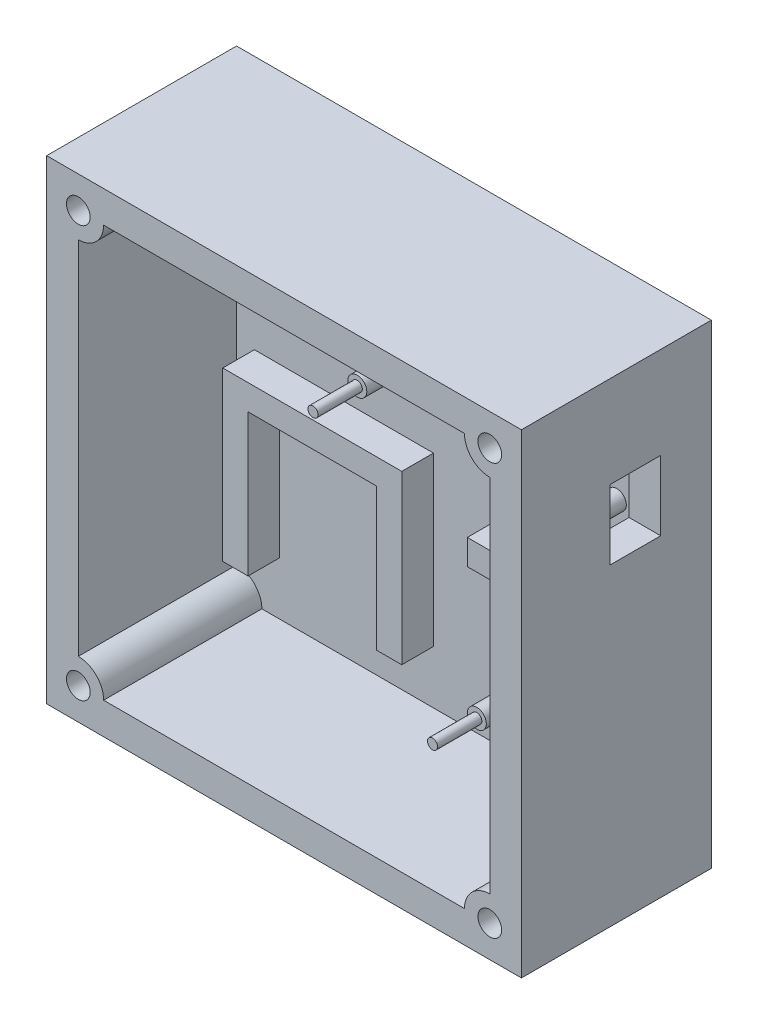
SolidWorks part; units mm, degrees
ref_plane "Front Plane" through (0, 0, 0) normal (0, 0, 1) x (1, 0, 0)
ref_plane "Top Plane" through (0, 0, 0) normal (0, 1, 0) x (1, 0, 0)
ref_plane "Right Plane" through (0, 0, 0) normal (1, 0, 0) x (0, 0, -1)
sketch "Sketch1" plane through (0, 0, 0) normal (0, 0, 1) x (1, 0, 0)
  line L1 (-47.625, -47.625) -> (47.625, -47.625)
  line L2 (-47.625, -47.625) -> (-47.625, 47.625)
  line L3 (-47.625, 47.625) -> (47.625, 47.625)
  line L4 (47.625, -47.625) -> (47.625, 47.625)
  line L5 (-47.625, -47.625) -> (47.625, 47.625) construction
  line L6 (-47.625, 47.625) -> (47.625, -47.625) construction
  point P0 (0, 0)
  dimension "D1" = 95.25
  dimension "D2" = 95.25
extrude "Boss-Extrude1" add sketch "Sketch1" along normal blind 38.1
shell "Shell1" thickness 6.35
ref_plane "Plane1" through (0, 0, 38.1) normal (0, 0, 1) x (1, 0, 0)
sketch "Sketch2" plane through (0, 0, 38.1) normal (0, 0, 1) x (1, 0, 0)
  line L0 (41.275, 41.275) -> (-41.275, 41.275) construction
  line L1 (-41.275, 41.275) -> (-41.275, -41.275) construction
  line L2 (-41.275, 41.275) -> (-36.195, 41.275)
  line L3 (-41.275, 41.275) -> (-41.275, 36.195)
  line L4 (41.275, 41.275) -> (-41.275, 41.275) construction
  line L5 (41.275, -41.275) -> (41.275, 41.275) construction
  line L6 (36.195, 41.275) -> (41.275, 41.275)
  line L7 (41.275, 41.275) -> (41.275, 36.195)
  line L8 (-41.275, -41.275) -> (41.275, -41.275) construction
  line L9 (41.275, -36.195) -> (41.275, -41.275)
  line L10 (41.275, -41.275) -> (36.195, -41.275)
  line L11 (-41.275, -41.275) -> (41.275, -41.275) construction
  line L12 (-41.275, -36.195) -> (-41.275, -41.275)
  line L13 (-41.275, -41.275) -> (-36.195, -41.275)
  arc A0 (-36.195, 41.275) -> (-41.275, 36.195) centre (-41.275, 41.275) cw
  arc A1 (36.195, 41.275) -> (41.275, 36.195) centre (41.275, 41.275) ccw
  arc A2 (41.275, -36.195) -> (36.195, -41.275) centre (41.275, -41.275) ccw
  arc A3 (-41.275, -36.195) -> (-36.195, -41.275) centre (-41.275, -41.275) cw
  dimension "D1" = 5.08
extrude "Boss-Extrude2" add sketch "Sketch2" against normal up to surface (31.75 mm away) up to face at (0, 0, 6.35)
sketch "Sketch3" plane through (0, 0, 6.35) normal (0, 0, 1) x (1, 0, 0)
  line L0 (41.275, -36.195) -> (41.275, 36.195) construction
  circle A0 centre (35.0157, 31.115) radius 1.905
  circle A1 centre (-10.7043, 31.115) radius 1.016
  circle A2 centre (-10.7043, 13.335) radius 1.905
  circle A3 centre (35.0157, 13.335) radius 1.905
  dimension "D1" = 3.81
  dimension "D2" = 2.032
  dimension "D3" = 6.2593
  dimension "D4" = 17.78
  dimension "D5" = 45.72
  dimension "D6" = 10.16
extrude "Boss-Extrude3" add sketch "Sketch3" along normal blind 6.35
ref_plane "Plane2" through (0, 0, 12.7) normal (0, 0, 1) x (1, 0, 0)
sketch "Sketch4" plane through (0, 0, 12.7) normal (0, 0, 1) x (1, 0, 0)
  circle A0 centre (-10.7043, 31.115) radius 1.016
  circle A1 centre (-10.7043, 13.335) radius 1.016
  circle A2 centre (35.0157, 31.115) radius 1.016
  circle A3 centre (35.0157, 13.335) radius 1.016
  dimension "D1" = 2.032
extrude "Boss-Extrude4" add sketch "Sketch4" along normal blind 8.89
ref_plane "Plane3" through (0, 0, 6.35) normal (0, 0, 1) x (1, 0, 0)
sketch "Sketch5" plane through (0, 0, 6.35) normal (0, 0, 1) x (1, 0, 0)
  line L0 (-36.195, -41.275) -> (36.195, -41.275) construction
  line L5 (11.3665, -6.985) -> (11.3665, -40.6427) construction
  line L6 (11.3665, -6.985) -> (35.56, -6.985)
  line L7 (11.3665, -6.985) -> (11.3665, -1.905)
  line L8 (11.3665, -1.905) -> (35.56, -1.905)
  line L9 (35.56, -6.985) -> (35.56, -1.905)
  line L10 (11.3665, -6.985) -> (35.56, -1.905) construction
  line L11 (11.3665, -1.905) -> (35.56, -6.985) construction
  line L12 (35.56, -6.985) -> (35.56, -28.5697) construction
  line L13 (41.275, -36.195) -> (41.275, 36.195) construction
  circle A0 centre (13.2715, -32.385) radius 1.905
  circle A1 centre (33.655, -32.385) radius 1.905
  point P4 (23.4633, -4.445)
  dimension "D4" = 3.81
  dimension "D3" = 20.3835
  dimension "D1" = 8.89
  dimension "D2" = 25.4
  dimension "D5" = 5.08
  dimension "D6" = 7.62
extrude "Boss-Extrude5" add sketch "Sketch5" along normal blind 6.35
ref_plane "Plane4" through (0, 0, 12.7) normal (0, 0, 1) x (1, 0, 0)
sketch "Sketch7" plane through (0, 0, 12.7) normal (0, 0, 1) x (1, 0, 0)
  circle A0 centre (13.2715, -32.385) radius 1.016
  circle A1 centre (33.655, -32.385) radius 1.016
  dimension "D1" = 2.032
extrude "Boss-Extrude6" add sketch "Sketch7" along normal blind 8.89
ref_plane "Plane5" through (0, 0, 38.1) normal (0, 0, 1) x (1, 0, 0)
sketch "Sketch8" plane through (0, 0, 38.1) normal (0, 0, 1) x (1, 0, 0)
  circle A0 centre (-41.275, 41.275) radius 2.3812
  circle A1 centre (41.275, 41.275) radius 2.3812
  circle A2 centre (41.275, -41.275) radius 2.3812
  circle A3 centre (-41.275, -41.275) radius 2.3812
  arc A4 (-36.195, -41.275) -> (-41.275, -36.195) centre (-41.275, -41.275) ccw construction
  arc A5 (-41.275, 36.195) -> (-36.195, 41.275) centre (-41.275, 41.275) ccw construction
  arc A6 (36.195, 41.275) -> (41.275, 36.195) centre (41.275, 41.275) ccw construction
  arc A7 (41.275, -36.195) -> (36.195, -41.275) centre (41.275, -41.275) ccw construction
  dimension "D1" = 4.7625
extrude "Cut-Extrude1" cut sketch "Sketch8" against normal blind 8.89
ref_plane "Plane7" through (0, 0, 6.35) normal (0, 0, 1) x (1, 0, 0)
sketch "Sketch10" plane through (0, 0, 6.35) normal (0, 0, 1) x (1, 0, 0)
  line L0 (-37.6969, -30.607) -> (-37.6969, 2.9972)
  line L1 (-37.6969, 2.9972) -> (-1.7813, 2.9972)
  line L2 (-1.7813, 2.9972) -> (-1.7813, -30.607)
  line L3 (-1.7813, -30.607) -> (-6.8613, -30.607)
  line L4 (-6.8613, -30.607) -> (-6.8613, -2.0828)
  line L5 (-6.8613, -2.0828) -> (-32.6169, -2.0828)
  line L6 (-32.6169, -2.0828) -> (-32.6169, -30.607)
  line L7 (-32.6169, -30.607) -> (-37.6969, -30.607)
  line L8 (-36.195, -41.275) -> (36.195, -41.275) construction
  line L9 (-41.275, 36.195) -> (-41.275, -36.195) construction
  dimension "D1" = 5.08
  dimension "D2" = 25.7556
  dimension "D3" = 28.5242
  dimension "D4" = 5.08
  dimension "D5" = 10.668
  dimension "D6" = 3.5781
extrude "Boss-Extrude7" add sketch "Sketch10" along normal blind 6.35
ref_plane "Plane8" through (47.625, 0, 0) normal (1, 0, 0) x (0, 0, -1)
sketch "Sketch12" plane through (47.625, 0, 0) normal (1, 0, 0) x (0, 0, -1)
  line L0 (-10.16, 29.21) -> (-10.16, 33.02) construction
  line L1 (-10.16, 15.24) -> (-20.32, 15.24)
  line L2 (-10.16, 15.24) -> (-10.16, 29.21)
  line L3 (-10.16, 29.21) -> (-20.32, 29.21)
  line L4 (-20.32, 15.24) -> (-20.32, 29.21)
  line L5 (-10.16, 15.24) -> (-20.32, 29.21) construction
  line L6 (-10.16, 29.21) -> (-20.32, 15.24) construction
  line L7 (-12.7, 15.24) -> (-12.7, 11.43) construction
  line L8 (-6.35, 33.02) -> (-12.7, 33.02) construction
  line L10 (-38.1, 47.625) -> (0, 47.625) construction
  point P0 (-15.24, 22.225)
  dimension "D1" = 10.16
  dimension "D2" = 13.97
  dimension "D3" = 2.54
  dimension "D4" = 25.4
extrude "Cut-Extrude2" cut sketch "Sketch12" against normal up to surface (6.35 mm away) contours L4 L3 L2 L1 up to face at (41.275, 0, 22.225)
